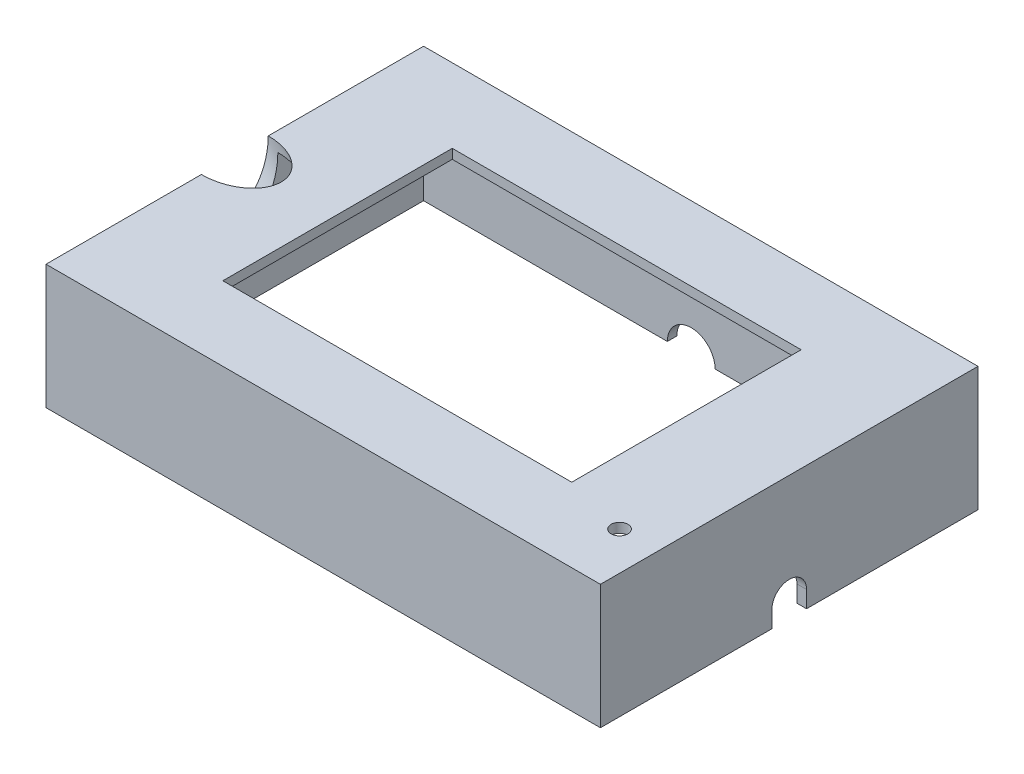
SolidWorks part; units mm, degrees
ref_plane "Front Plane" through (0, 0, 0) normal (0, 0, 1) x (1, 0, 0)
ref_plane "Top Plane" through (0, 0, 0) normal (0, 1, 0) x (1, 0, 0)
ref_plane "Right Plane" through (0, 0, 0) normal (1, 0, 0) x (0, 0, -1)
sketch "Sketch1" plane through (0, 0, 0) normal (0, 1, 0) x (1, 0, 0)
  line L0 (58, 39.5) -> (-58, 39.5)
  line L1 (56, -37.5) -> (-56, -37.5)
  line L2 (56, -37.5) -> (56, 37.5)
  line L3 (56, 37.5) -> (-56, 37.5)
  line L4 (-56, -37.5) -> (-56, 37.5)
  line L5 (56, -37.5) -> (-56, 37.5) construction
  line L6 (56, 37.5) -> (-56, -37.5) construction
  line L7 (-58, -39.5) -> (-58, 39.5)
  line L8 (58, -39.5) -> (-58, -39.5)
  line L9 (58, -39.5) -> (58, 39.5)
  point P0 (0, 0)
  dimension "D1" = 112
  dimension "D2" = 75
  dimension "D3" = 2
extrude "Boss-Extrude1" add sketch "Sketch1" along normal blind 24
sketch "Sketch2" plane through (0, 24, 0) normal (0, 1, 0) x (1, 0, 0)
  line L1 (58, -39.5) -> (-58, -39.5)
  line L2 (58, -39.5) -> (58, 39.5)
  line L3 (58, 39.5) -> (-58, 39.5)
  line L4 (-58, -39.5) -> (-58, 39.5)
  line L5 (58, -39.5) -> (-58, 39.5) construction
  line L6 (58, 39.5) -> (-58, -39.5) construction
  point P0 (0, 0)
extrude "Boss-Extrude2" add sketch "Sketch2" along normal blind 2
sketch "Sketch3" plane through (0, 26, 0) normal (0, 1, 0) x (1, 0, 0)
  line L1 (-36.5, 24) -> (36.5, 24)
  line L2 (-36.5, 24) -> (-36.5, -24)
  line L3 (-36.5, -24) -> (36.5, -24)
  line L4 (36.5, 24) -> (36.5, -24)
  line L5 (-36.5, 24) -> (36.5, -24) construction
  line L6 (-36.5, -24) -> (36.5, 24) construction
  point P0 (0, 0)
  dimension "D1" = 48
  dimension "D2" = 73
extrude "Cut-Extrude1" cut sketch "Sketch3" against normal up to surface (2 mm away) up to face at (0, 24, 0)
sketch "Sketch4" plane through (0, 26, 0) normal (0, 1, 0) x (1, 0, 0)
  line L0 (-58, -39.5) -> (58, -39.5) construction
  line L1 (58, -39.5) -> (58, 39.5) construction
  circle A0 centre (50, -27.5) radius 1.75
  dimension "D1" = 3.5
  dimension "D2" = 12
  dimension "D3" = 8
extrude "Cut-Extrude2" cut sketch "Sketch4" against normal up to surface (2 mm away) up to face at (0, 24, 0)
sketch "Sketch5" plane through (0, 0, 0) normal (0, -1, 0) x (1, 0, 0)
  line L0 (-58, -0.8295) -> (-85, -0.8295) construction
  line L1 (-58, -39.5) -> (-58, 39.5) construction
  dimension "D1" = 27
ref_plane "Plane1" through (-40.8968, 42.4698, 0) normal (0.6936, -0.7203, 0) x (-0.7203, -0.6936, 0)
sketch "Sketch6" plane through (-40.8968, 42.4698, 0) normal (0.6936, -0.7203, 0) x (-0.7203, -0.6936, 0)
  line L0 (23.7439, 39.5) -> (23.7439, -39.5) construction
  circle A0 centre (23.7439, 0) radius 7
  dimension "D1" = 14
extrude "Cut-Extrude3" cut sketch "Sketch6" along normal blind 10
sketch "Sketch7" plane through (58, 0, 0) normal (1, 0, 0) x (0, 0, -1)
  line L1 (0, 3.5) -> (0, 0) construction
  line L2 (-39.5, 0) -> (39.5, 0) construction
  line L3 (-3.625, 3.5) -> (-3.625, 0)
  line L4 (3.625, 3.5) -> (3.625, 0)
  line L5 (3.625, 0) -> (-3.625, 0)
  arc A0 (3.625, 3.5) -> (-3.625, 3.5) centre (0, 3.5) ccw
  dimension "D1" = 7.25
  dimension "D2" = 3.5
extrude "Cut-Extrude4" cut sketch "Sketch7" against normal up to surface (2 mm away) up to face at (56, 12, 0)
sketch "Sketch8" plane through (0, 0, -39.5) normal (0, 0, -1) x (-1, 0, 0)
  line L0 (-58, 0) -> (58, 0) construction
  circle A0 centre (0, 0) radius 5
  dimension "D1" = 10
extrude "Cut-Extrude5" cut sketch "Sketch8" against normal up to surface (2 mm away) up to face at (0, 12, -37.5)
